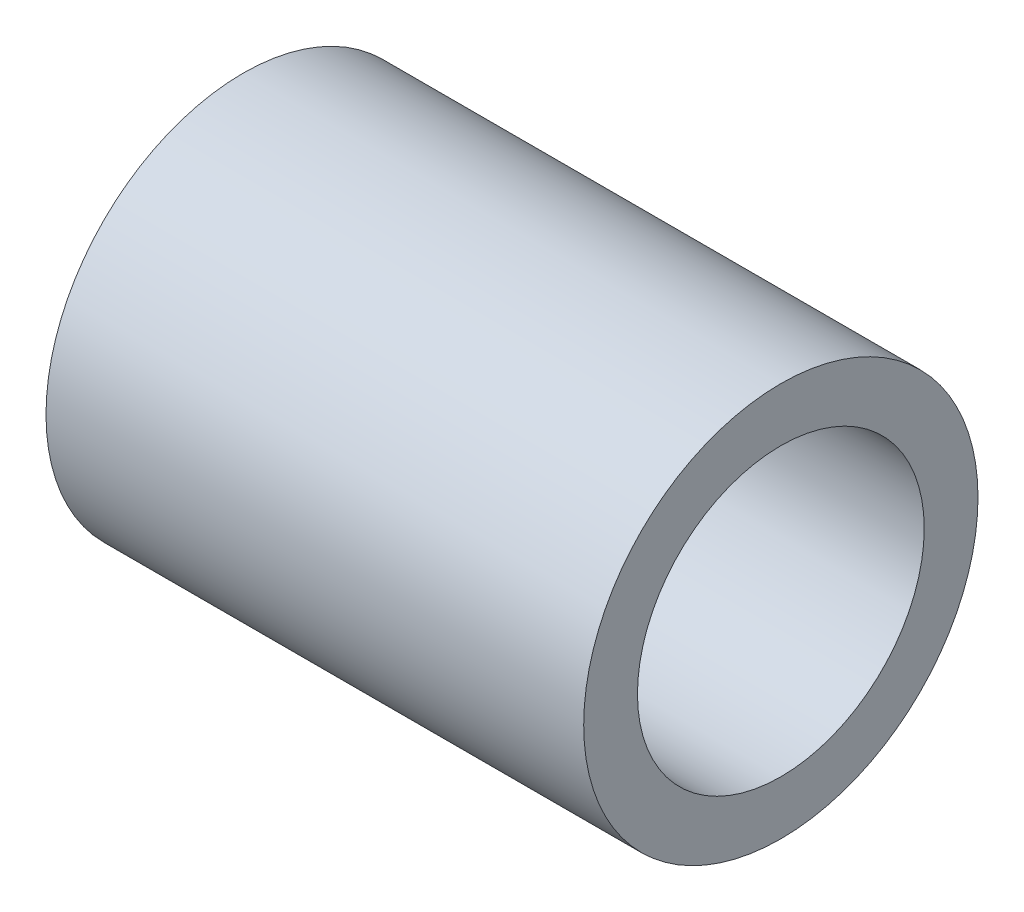
SolidWorks part; units mm, degrees
material "黄铜"
ref_plane "前视基准面" through (0, 0, 0) normal (0, 0, 1) x (1, 0, 0)
ref_plane "上视基准面" through (0, 0, 0) normal (0, 1, 0) x (1, 0, 0)
ref_plane "右视基准面" through (0, 0, 0) normal (1, 0, 0) x (0, 0, -1)
sketch "草图1" plane through (0, 0, 0) normal (1, 0, 0) x (0, 0, -1)
  circle A0 centre (0, 0) radius 8
  circle A1 centre (0, 0) radius 11
  dimension "D1" = 16
  dimension "D2" = 22
extrude "凸台-拉伸1" add sketch "草图1" against normal blind 30
